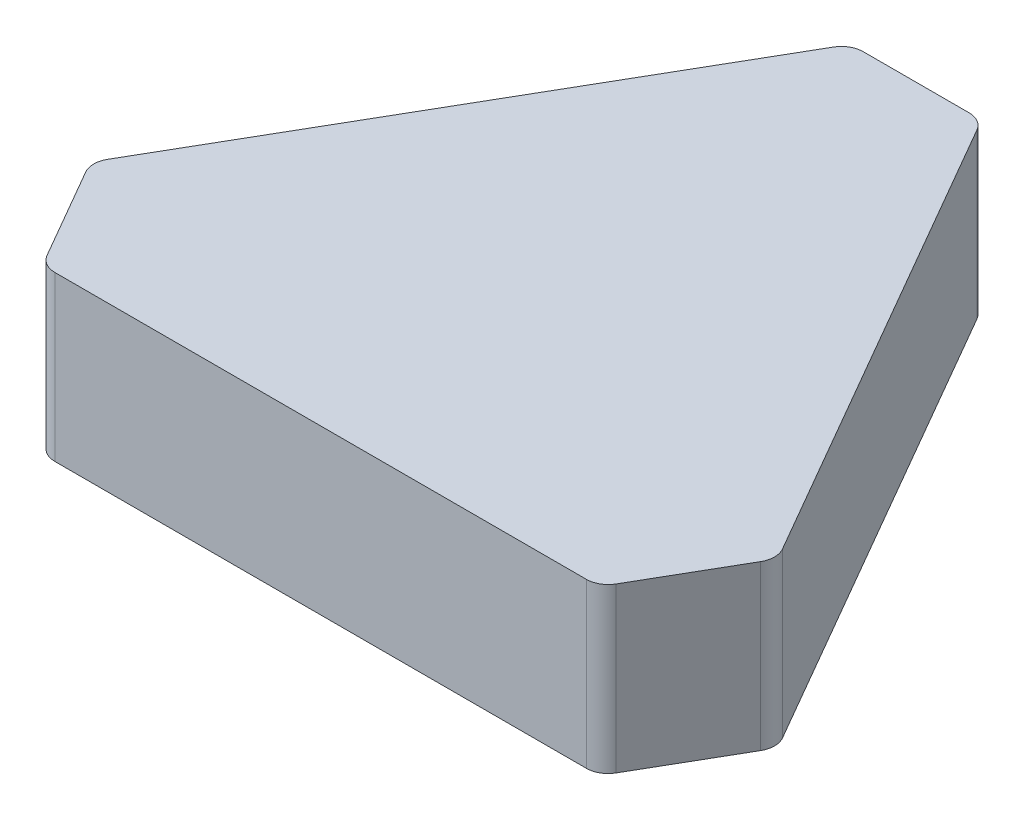
SolidWorks part; units mm, degrees
ref_plane "Front Plane" through (0, 0, 0) normal (0, 0, 1) x (1, 0, 0)
ref_plane "Top Plane" through (0, 0, 0) normal (0, 1, 0) x (1, 0, 0)
ref_plane "Right Plane" through (0, 0, 0) normal (1, 0, 0) x (0, 0, -1)
sketch "Sketch2" plane through (0, 0, 0) normal (0, 1, 0) x (1, 0, 0)
  line L0 (0, 0) -> (75, 0) construction
  line L1 (0, 0) -> (37.5, 64.9519)
  line L2 (37.5, 64.9519) -> (75, 0)
  line L3 (75, 0) -> (0, 0)
  circle A0 centre (37.5, 21.6506) radius 21.6506
  dimension "D1" = 60
  dimension "D2" = 60
  dimension "D3" = 75
extrude "Boss-Extrude1" add sketch "Sketch2" along normal blind 15 contours A0 | A0 L1 L3 | A0 L2 L1 | A0 L3 L2
sketch "Sketch3" plane through (0, 15, 0) normal (0, 1, 0) x (1, 0, 0)
  line L0 (31.5, 54.5596) -> (43.5, 54.5596)
  line L1 (0, 0) -> (37.5, 64.9519) construction
  line L2 (37.5, 64.9519) -> (75, 0) construction
  line L3 (43.5, 54.5596) -> (37.5, 64.9519)
  line L4 (37.5, 64.9519) -> (31.5, 54.5596)
  line L5 (0, 0) -> (6, 10.3923)
  line L6 (6, 10.3923) -> (12, 0)
  line L7 (75, 0) -> (0, 0) construction
  line L8 (12, 0) -> (0, 0)
  line L9 (75, 0) -> (69, 10.3923)
  line L10 (69, 10.3923) -> (63, 0)
  line L11 (63, 0) -> (75, 0)
  dimension "D1" = 12
  dimension "D2" = 12
  dimension "D3" = 12
extrude "Cut-Extrude1" cut sketch "Sketch3" against normal through all both and the other way through all
fillet "Fillet1" radius 2 6 edges at (63, 7.5, 0) (69, 7.5, -10.3923) (43.5, 7.5, -54.5596) (31.5, 7.5, -54.5596) (6, 7.5, -10.3923) (12, 7.5, 0)
sketch "Sketch4" plane through (0, 0, 0) normal (0, -1, 0) x (1, 0, 0)
  line L0 (44.0774, -53.5596) -> (68.4226, -11.3923) construction
  line L1 (61.8453, 0) -> (13.1547, 0) construction
  line L2 (6.5774, -11.3923) -> (30.9226, -53.5596) construction
  circle A0 centre (37.5, -21.6506) radius 21.6506 construction
  circle A1 centre (37.5, -21.6506) radius 13.6506
  dimension "D1" = 8
extrude "Cut-Extrude2" cut sketch "Sketch4" against normal blind 3
